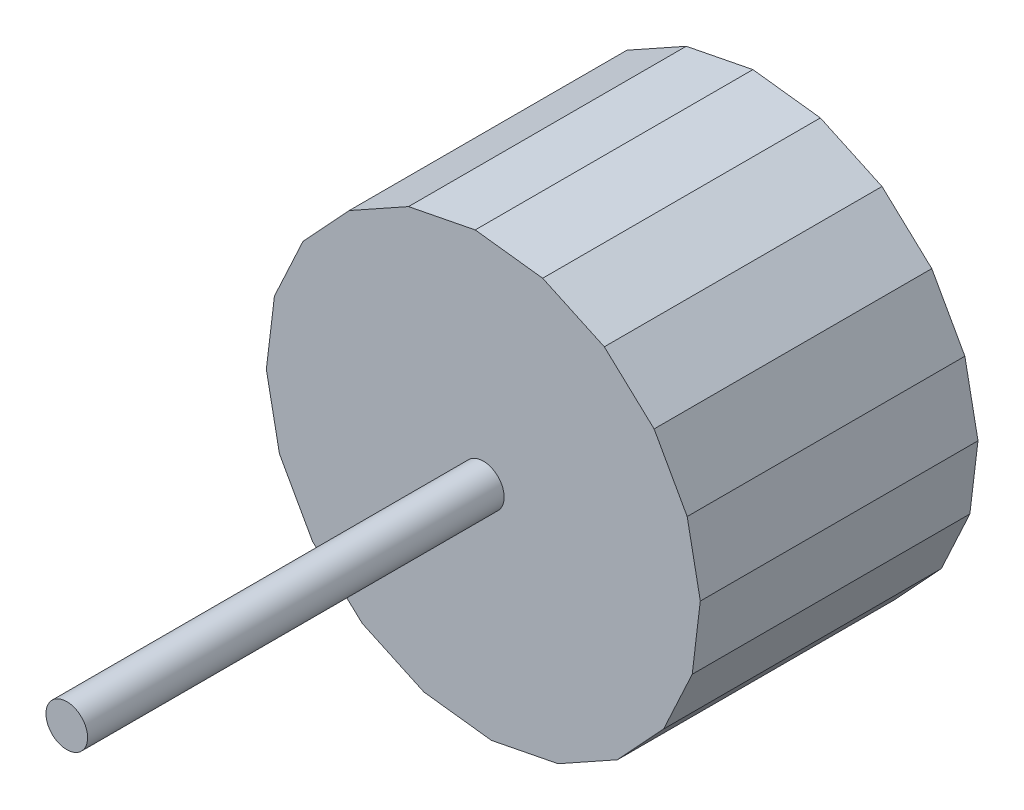
SolidWorks part; units mm, degrees
ref_plane "Plano frontal" through (0, 0, 0) normal (0, 0, 1) x (1, 0, 0)
ref_plane "Plano superior" through (0, 0, 0) normal (0, 1, 0) x (1, 0, 0)
ref_plane "Plano direito" through (0, 0, 0) normal (1, 0, 0) x (0, 0, -1)
sketch "Esboço1" plane through (0, 0, 0) normal (0, 0, 1) x (1, 0, 0)
  line L0 (-12.9869, 8.7143) -> (-15.0442, 4.2746)
  line L1 (12.3009, 9.6584) -> (8.7143, 12.9869)
  line L2 (8.7143, 12.9869) -> (4.2746, 15.0442)
  line L3 (4.2746, 15.0442) -> (-0.5835, 15.6288)
  line L4 (-0.5835, 15.6288) -> (-5.3845, 14.6835)
  line L5 (-5.3845, 14.6835) -> (-9.6584, 12.3009)
  line L6 (-9.6584, 12.3009) -> (-12.9869, 8.7143)
  line L7 (-15.0442, 4.2746) -> (-15.6288, -0.5835)
  line L8 (-15.6288, -0.5835) -> (-14.6835, -5.3845)
  line L9 (-14.6835, -5.3845) -> (-12.3009, -9.6584)
  line L10 (-12.3009, -9.6584) -> (-8.7143, -12.9869)
  line L11 (-8.7143, -12.9869) -> (-4.2746, -15.0442)
  line L12 (-4.2746, -15.0442) -> (0.5835, -15.6288)
  line L13 (0.5835, -15.6288) -> (5.3845, -14.6835)
  line L14 (5.3845, -14.6835) -> (9.6584, -12.3009)
  line L15 (9.6584, -12.3009) -> (12.9869, -8.7143)
  line L16 (12.9869, -8.7143) -> (15.0442, -4.2746)
  line L17 (15.0442, -4.2746) -> (15.6288, 0.5835)
  line L18 (15.6288, 0.5835) -> (14.6835, 5.3845)
  line L19 (14.6835, 5.3845) -> (12.3009, 9.6584)
  circle A0 centre (0, 0) radius 15.4471 construction
extrude "Ressalto-extrusão1" add sketch "Esboço1" along normal blind 20
shell "Casca1" thickness 1.5
sketch "Esboço2" plane through (0, 0, 20) normal (0, 0, 1) x (1, 0, 0)
  circle A0 centre (0, 0) radius 1.5
extrude "Ressalto-extrusão2" add sketch "Esboço2" along normal blind 30
